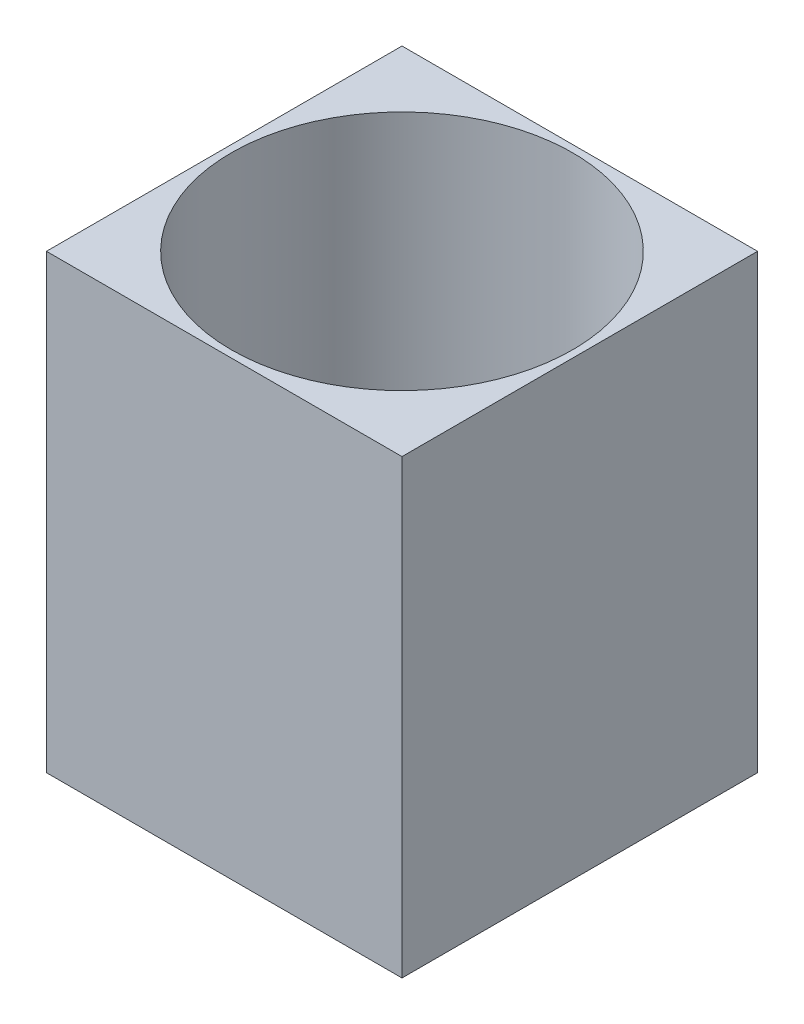
SolidWorks part; units mm, degrees
ref_plane "Front Plane" through (0, 0, 0) normal (0, 0, 1) x (1, 0, 0)
ref_plane "Top Plane" through (0, 0, 0) normal (0, 1, 0) x (1, 0, 0)
ref_plane "Right Plane" through (0, 0, 0) normal (1, 0, 0) x (0, 0, -1)
sketch "Sketch1" plane through (0, 0, 0) normal (0, 1, 0) x (1, 0, 0)
  line L1 (0, 0) -> (5, 0)
  line L2 (0, 0) -> (0, 5)
  line L3 (0, 5) -> (5, 5)
  line L4 (5, 0) -> (5, 5)
  circle A0 centre (2.5, 2.5) radius 2.4
  point P8 (2.5, 5)
  point P10 (0, 2.5)
  dimension "D3" = 4.8
  dimension "D1" = 5
  dimension "D2" = 5
extrude "Boss-Extrude1" add sketch "Sketch1" along normal blind 6.35
